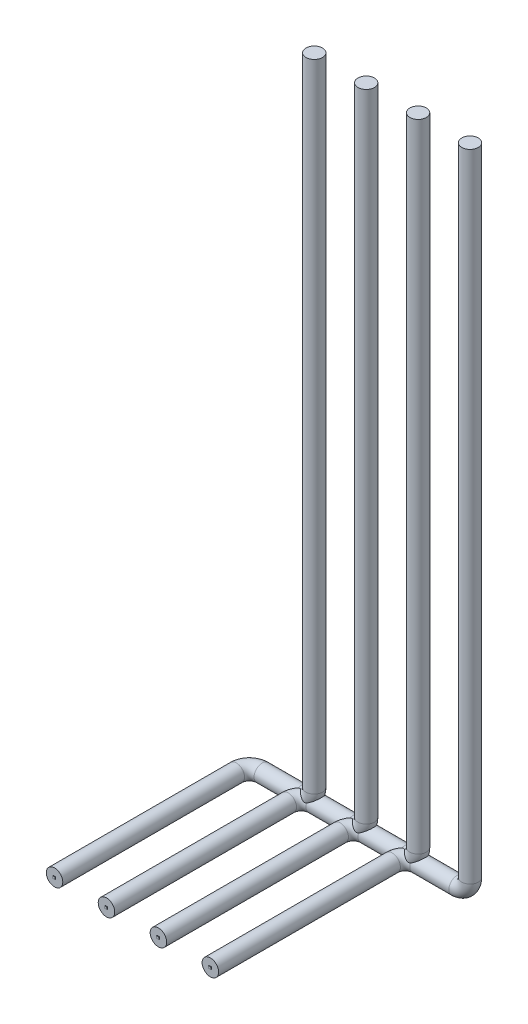
SolidWorks part; units mm, degrees
ref_plane "Alzado" through (0, 0, 0) normal (0, 0, 1) x (1, 0, 0)
ref_plane "Planta" through (0, 0, 0) normal (0, 1, 0) x (1, 0, 0)
ref_plane "Vista lateral" through (0, 0, 0) normal (1, 0, 0) x (0, 0, -1)
sketch3d "Croquis3D1"
  line L0 (0, 0, 0) -> (0, 0, -280)
  line L1 (20, 0, -300) -> (80, 0, -300)
  line L2 (100, 20, -300) -> (100, 1000, -300)
  arc A0 (80, 0, -300) -> (100, 20, -300) centre (80, 20, -300) ccw
  arc A1 (0, 0, -280) -> (20, 0, -300) centre (20, 0, -280) ccw
  point P7 (100, 0, -300)
  point P8 (80, 20, -280)
  point P11 (0, 0, -300)
  point P12 (20, -20, -280)
  dimension "D4" = 20
  dimension "D1" = 300
  dimension "D2" = 100
  dimension "D3" = 1000
sketch "Croquis2" plane through (0, 0, 0) normal (0, 0, 1) x (1, 0, 0)
  circle A0 centre (0, 0) radius 12.7
  dimension "D1" = 25.4
sweep "Barrer1" add profiles "Croquis2" path "Croquis3D1"
sketch "Croquis3" plane through (0, 0, 0) normal (0, 0, 1) x (1, 0, 0)
  line L1 (-1.8117, -1.6563) -> (1.8117, -1.6563)
  line L2 (-1.8117, -1.6563) -> (-1.8117, 1.6563)
  line L3 (-1.8117, 1.6563) -> (1.8117, 1.6563)
  line L4 (1.8117, -1.6563) -> (1.8117, 1.6563)
  line L5 (-1.8117, -1.6563) -> (1.8117, 1.6563) construction
  line L6 (-1.8117, 1.6563) -> (1.8117, -1.6563) construction
  point P0 (0, 0)
extrude "Saliente-Extruir1" add sketch "Croquis3" along normal blind 1
pattern_linear "MatrizL1" count 4 spacing 80 along (1, 0, 0) of bodies 102
